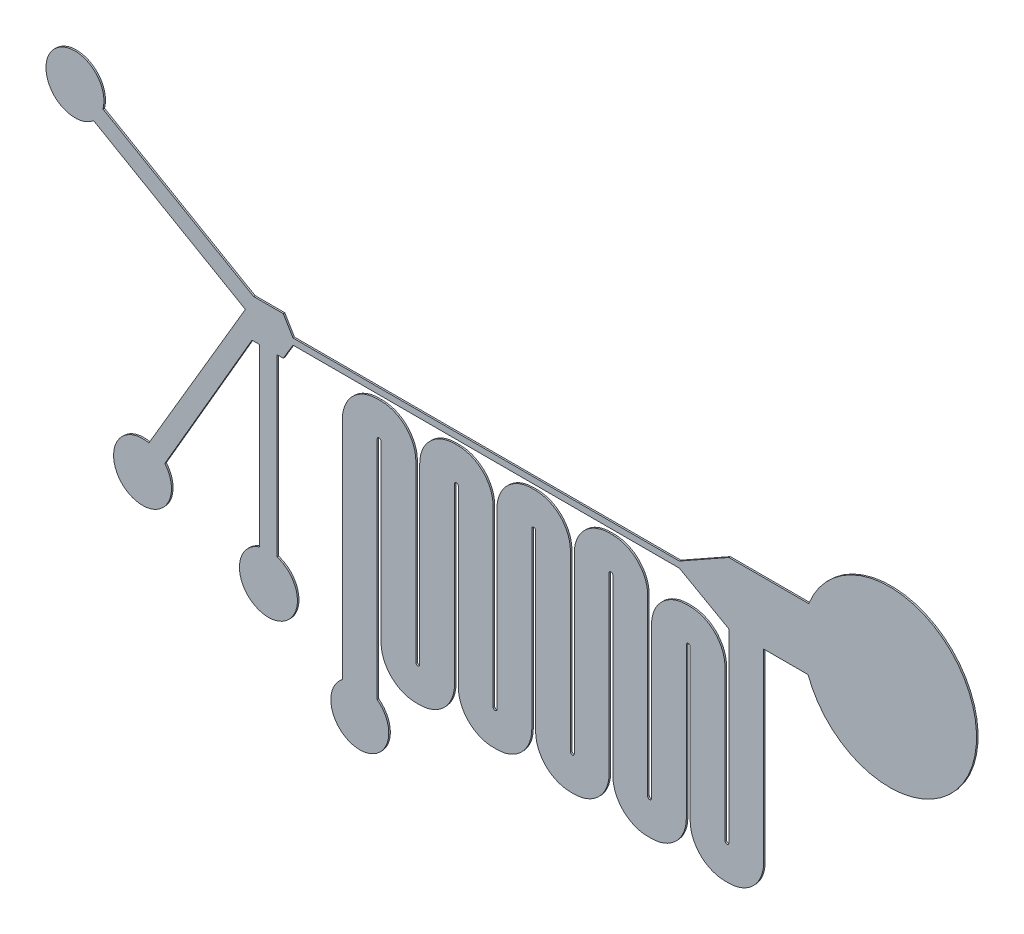
SolidWorks part; units mm, degrees
ref_plane "Front Plane" through (0, 0, 0) normal (0, 0, 1) x (1, 0, 0)
ref_plane "Top Plane" through (0, 0, 0) normal (0, 1, 0) x (1, 0, 0)
ref_plane "Right Plane" through (0, 0, 0) normal (1, 0, 0) x (0, 0, -1)
sketch "Sketch1" plane through (0, 0, 0) normal (0, 0, 1) x (1, 0, 0)
  line L18 (-1.3151, 0.6931) -> (-1.0651, 0.2731)
  line L19 (-1.0651, 0.1131) -> (-1.3151, -0.3069)
  line L27 (-1.0651, 0.2731) -> (8.9349, 0.2731)
  line L28 (-1.0651, 0.1131) -> (8.9349, 0.1131)
  line L77 (-1.6255, 0.6931) -> (-1.3151, 0.6931)
  line L78 (-1.4751, -0.3069) -> (-1.3151, -0.3069)
  line L79 (-1.4751, -0.3069) -> (-1.4751, -4.8226)
  line L80 (-1.9251, -0.3069) -> (-1.9251, -4.8069)
  line L81 (-1.9251, -4.8069) -> (-1.9251, -4.8415)
  line L82 (-2.1251, -0.3069) -> (-4.3452, -4.1364)
  line L83 (-2.1251, -0.3069) -> (-1.9251, -0.3069)
  line L89 (8.9349, 0.2731) -> (10.2149, 0.9931)
  line L91 (-2.2969, 0.2969) -> (-6.1928, 2.5462)
  line L93 (-5.9802, 2.9431) -> (-2.4219, 0.8887)
  line L94 (-1.6255, 0.6931) -> (-2.083, 0.6931)
  line L95 (-4.3452, -4.1364) -> (-4.3808, -4.1977) construction
  line L96 (-1.4751, -4.8226) -> (-1.4751, -4.8415)
  line L97 (8.9349, 0.1131) -> (10.2149, -0.6069)
  line L101 (10.2149, 0.9931) -> (10.5145, 0.9931)
  line L102 (10.5145, 0.9931) -> (10.9354, 0.9931)
  line L110 (-2.4219, 0.8887) -> (-2.083, 0.6931)
  line L111 (10.9354, 0.9931) -> (12.2827, 0.9931)
  line L113 (-2.2969, 0.2969) -> (-4.795, -3.9447)
  line L114 (-4.3452, -4.1364) -> (-4.3808, -4.1977)
  line L123 (11.1149, -0.6069) -> (12.2649, -0.6069)
  line L129 (-5.9802, 2.9431) -> (-5.9824, 2.9454)
  line L134 (-6.1928, 2.5462) -> (-6.2246, 2.5625)
  line L160 (-0.5195, 0.1131) -> (-0.5195, 0.0131) construction
  line L165 (9.2149, -0.6069) -> (9.1149, -0.6069) construction
  line L192 (10.2149, -6.3069) -> (10.1149, -6.3069)
  line L202 (9.2149, -0.6069) -> (9.1149, -0.6069)
  line L212 (8.2149, -6.3069) -> (8.1149, -6.3069)
  line L216 (2.1148, -0.9043) -> (2.115, -5.4113)
  line L221 (7.2149, -0.0043) -> (7.1149, -0.0043)
  line L229 (6.2149, -6.3113) -> (6.1149, -6.3113)
  line L237 (5.2149, -0.0043) -> (5.1148, -0.0043)
  line L245 (4.2148, -6.3113) -> (4.1149, -6.3113)
  line L253 (3.2149, -0.0043) -> (3.1148, -0.0043)
  line L261 (2.2148, -6.3113) -> (2.1286, -6.3113)
  line L282 (1.1148, 0) -> (1.2148, 0)
  line L286 (1.2148, -0.9) -> (1.2148, -5.4113)
  line L296 (2.2148, -0.9043) -> (2.2148, -5.4113)
  line L298 (3.1148, -0.9043) -> (3.1148, -5.4113)
  line L300 (3.2149, -0.9043) -> (3.2149, -5.4113)
  line L302 (4.1149, -0.9043) -> (4.1149, -5.4113)
  line L304 (4.2148, -5.4113) -> (4.2148, -0.9043)
  line L306 (5.1148, -5.4113) -> (5.1148, -0.9043)
  line L308 (5.2149, -0.9043) -> (5.2149, -5.4113)
  line L310 (6.1149, -0.9043) -> (6.1149, -5.4113)
  line L312 (6.2149, -5.4113) -> (6.2149, -0.9043)
  line L314 (7.1149, -5.4113) -> (7.1149, -0.9043)
  line L316 (7.2149, -0.9043) -> (7.2149, -5.4069)
  line L318 (8.1149, -0.9043) -> (8.1149, -5.4069)
  line L320 (8.2149, -5.4069) -> (8.2149, -1.5069)
  line L322 (9.1149, -5.4069) -> (9.1149, -1.5069)
  line L324 (9.2149, -1.5069) -> (9.2149, -5.4069)
  line L326 (10.1149, -1.5069) -> (10.1149, -5.4069)
  line L328 (10.2149, -0.6069) -> (10.2149, -5.4069)
  line L330 (11.1149, -0.6069) -> (11.1149, -5.4069)
  line L333 (0.2148, -0.9) -> (0.2148, -6.5929)
  line L334 (1.1148, -0.9) -> (1.1148, -6.5929)
  line L336 (0.2148, -6.5929) -> (0.2148, -6.7429)
  line L337 (1.1148, -6.5929) -> (1.1148, -6.7429)
  arc A10 (-1.9251, -4.8415) -> (-1.4751, -4.8415) centre (-1.7001, -5.5569) ccw
  arc A11 (-4.795, -3.9447) -> (-4.3808, -4.1977) centre (-4.9579, -4.6768) ccw
  arc A15 (12.2649, -0.6069) -> (12.2827, 0.9931) centre (14.3766, 0.1696) ccw
  arc A17 (-5.9824, 2.9454) -> (-6.2246, 2.5625) centre (-6.7077, 3.1362) ccw
  arc A25 (9.2149, -5.4069) -> (10.1149, -6.3069) centre (10.1149, -5.4069) ccw
  arc A26 (10.1149, -1.5069) -> (9.2149, -0.6069) centre (9.2149, -1.5069) ccw
  arc A28 (8.2149, -6.3069) -> (9.1149, -5.4069) centre (8.2149, -5.4069) ccw
  arc A29 (7.2149, -5.4069) -> (8.1149, -6.3069) centre (8.1149, -5.4069) ccw
  arc A30 (8.1149, -0.9043) -> (7.2149, -0.0043) centre (7.2149, -0.9043) ccw
  arc A33 (5.2149, -5.4113) -> (6.1149, -6.3113) centre (6.1149, -5.4113) ccw
  arc A34 (6.1149, -0.9043) -> (5.2149, -0.0043) centre (5.2149, -0.9043) ccw
  arc A37 (3.2149, -5.4113) -> (4.1149, -6.3113) centre (4.1149, -5.4113) ccw
  arc A38 (4.1149, -0.9043) -> (3.2149, -0.0043) centre (3.2149, -0.9043) ccw
  arc A39 (3.1148, -0.0043) -> (2.2148, -0.9043) centre (3.1148, -0.9043) ccw
  arc A41 (1.2148, -5.4113) -> (2.1286, -6.3113) centre (2.115, -5.4113) ccw
  arc A42 (2.1148, -0.9043) -> (1.2148, 0) centre (1.2148, -0.9) ccw
  arc A44 (10.2149, -6.3069) -> (11.1149, -5.4069) centre (10.2149, -5.4069) ccw
  arc A45 (9.1149, -0.6069) -> (8.2149, -1.5069) centre (9.1149, -1.5069) ccw
  arc A46 (7.1149, -0.0043) -> (6.2149, -0.9043) centre (7.1149, -0.9043) ccw
  arc A47 (6.2149, -6.3113) -> (7.1149, -5.4113) centre (6.2149, -5.4113) ccw
  arc A48 (5.1148, -0.0043) -> (4.2148, -0.9043) centre (5.1148, -0.9043) ccw
  arc A50 (4.2148, -6.3113) -> (5.1148, -5.4113) centre (4.2148, -5.4113) ccw
  arc A51 (2.2148, -6.3113) -> (3.1148, -5.4113) centre (2.2148, -5.4113) ccw
  arc A52 (2.115, -5.4113) -> (2.2148, -5.4113) centre (2.1649, -5.4113) ccw
  arc A53 (4.1149, -5.4113) -> (4.2148, -5.4113) centre (4.1649, -5.4113) ccw
  arc A54 (6.1149, -5.4113) -> (6.2149, -5.4113) centre (6.1649, -5.4113) ccw
  arc A55 (3.2149, -0.9043) -> (3.1148, -0.9043) centre (3.1649, -0.9043) ccw
  arc A56 (5.2149, -0.9043) -> (5.1148, -0.9043) centre (5.1649, -0.9043) ccw
  arc A57 (7.2149, -0.9043) -> (7.1149, -0.9043) centre (7.1649, -0.9043) ccw
  arc A58 (9.2149, -1.5069) -> (9.1149, -1.5069) centre (9.1649, -1.5069) ccw
  arc A59 (8.1149, -5.4069) -> (8.2149, -5.4069) centre (8.1649, -5.4069) ccw
  arc A60 (10.1149, -5.4069) -> (10.2149, -5.4069) centre (10.1649, -5.4069) ccw
  arc A61 (1.1148, 0) -> (0.2148, -0.9) centre (1.1148, -0.9) ccw
  arc A62 (1.2148, -0.9) -> (1.1148, -0.9) centre (1.1648, -0.9) ccw
  arc A63 (0.2148, -6.7429) -> (1.1148, -6.7429) centre (0.6648, -7.3429) ccw
  point P0 (-1.9251, -0.3069)
  point P2 (-1.3151, 0.6931)
  point P3 (-1.4751, -0.3069)
  point P10 (-1.7002, -4.8069)
  point P11 (-1.7002, -4.8069)
  point P13 (-1.7001, -5.5569)
  point P15 (11.1149, -0.6069)
  point P20 (-2.1251, -0.3069)
  point P23 (-4.5829, -4.0272)
  point P26 (1.1148, -0.9)
  point P29 (-4.9579, -4.6768)
  point P35 (-1.0651, 0.1131)
  point P37 (-1.3151, 0.6931)
  point P38 (-1.0651, 0.2731)
  point P39 (-1.3151, 0.6931)
  point P46 (-6.4316, 2.4239)
  point P48 (-7.0811, 2.7989)
  point P49 (-6.0729, 2.7368)
  point P51 (10.2149, -6.3069)
  point P55 (-1.7001, -6.3069)
  point P56 (-6.7077, 3.1362)
  point P58 (10.1149, -6.3069)
  point P61 (0.6648, -6.5929)
  point P62 (10.2149, -5.4069)
  point P65 (10.2149, -1.5069)
  point P68 (9.2149, -0.6069)
  point P76 (10.1149, -5.4069)
  point P79 (9.1149, -0.6069)
  point P83 (0.6648, -7.3429)
  point P85 (8.1149, -5.4069)
  point P88 (7.2149, -0.0043)
  point P90 (8.2148, -6.3069)
  point P91 (8.1148, -6.3069)
  point P95 (7.1149, -0.0043)
  point P103 (5.2149, -0.0043)
  point P104 (5.1149, -0.0043)
  point P107 (3.2149, -0.0043)
  point P108 (3.1149, -0.0043)
  point P111 (1.215, 0)
  point P112 (1.1148, 0)
  point P114 (6.2148, -6.3069)
  point P115 (6.1148, -6.3069)
  point P118 (4.2148, -6.3069)
  point P119 (4.1148, -6.3069)
  point P122 (2.2148, -6.3113)
  point P123 (2.1148, -6.3069)
  point P128 (6.2148, -5.4069)
  point P129 (6.1148, -5.4069)
  point P130 (5.2149, -5.4113)
  point P131 (5.1148, -5.4069)
  point P132 (4.2148, -5.4069)
  point P133 (4.1148, -5.4069)
  point P134 (3.2149, -5.4113)
  point P135 (3.1148, -5.4069)
  point P136 (2.2148, -5.4069)
  point P137 (2.1148, -5.4069)
  point P138 (1.2148, -5.4113)
  point P140 (6.2149, -0.9043)
  point P141 (6.1148, -0.8797)
  point P142 (5.2148, -0.8797)
  point P143 (5.1148, -0.8797)
  point P144 (4.2148, -0.9043)
  point P145 (4.1148, -0.8797)
  point P146 (3.2148, -0.8797)
  point P147 (3.1148, -0.9043)
  point P148 (2.2148, -0.9043)
  point P149 (2.1148, -0.8797)
  point P150 (1.2148, -0.8797)
  point P151 (1.1148, -0.8797)
  point P152 (-0.1038, -0.9083)
  dimension "D7" = 0.45
  dimension "D17" = 0.72
  dimension "D23" = 0.1
  dimension "D19" = 1.28
  dimension "D14" = 0.75
  dimension "D31" = 0.75
  dimension "D3" = 0.42
  dimension "D4" = 0.42
  dimension "D5" = 1.28
  dimension "D6" = 0.16
  dimension "D8" = 0.25
  dimension "D9" = 0.0345
  dimension "D10" = 0.225
  dimension "D11" = 10
  dimension "D12" = 10
  dimension "D13" = 0.2
  dimension "D15" = 0.75
  dimension "D16" = 0.25
  dimension "D18" = 0.72
  dimension "D20" = 0
  dimension "D21" = 0.9
  dimension "D22" = 1.15
  dimension "D24" = 0.9
  dimension "D25" = 4.5
  dimension "D26" = 0.1
  dimension "D27" = 0.45
  dimension "D28" = 0.16
  dimension "D29" = 0
  dimension "D30" = 0.9
  dimension "D32" = 1
  dimension "D33" = 4.5
  dimension "D34" = 0.1
  dimension "D36" = 0.1
  dimension "D38" = 0.1
  dimension "D43" = 0.1
  dimension "D47" = 0.1
  dimension "D54" = 5.4069
  dimension "D55" = 5.4069
extrude "Boss-Extrude1" add sketch "Sketch1" along normal blind 0.04
